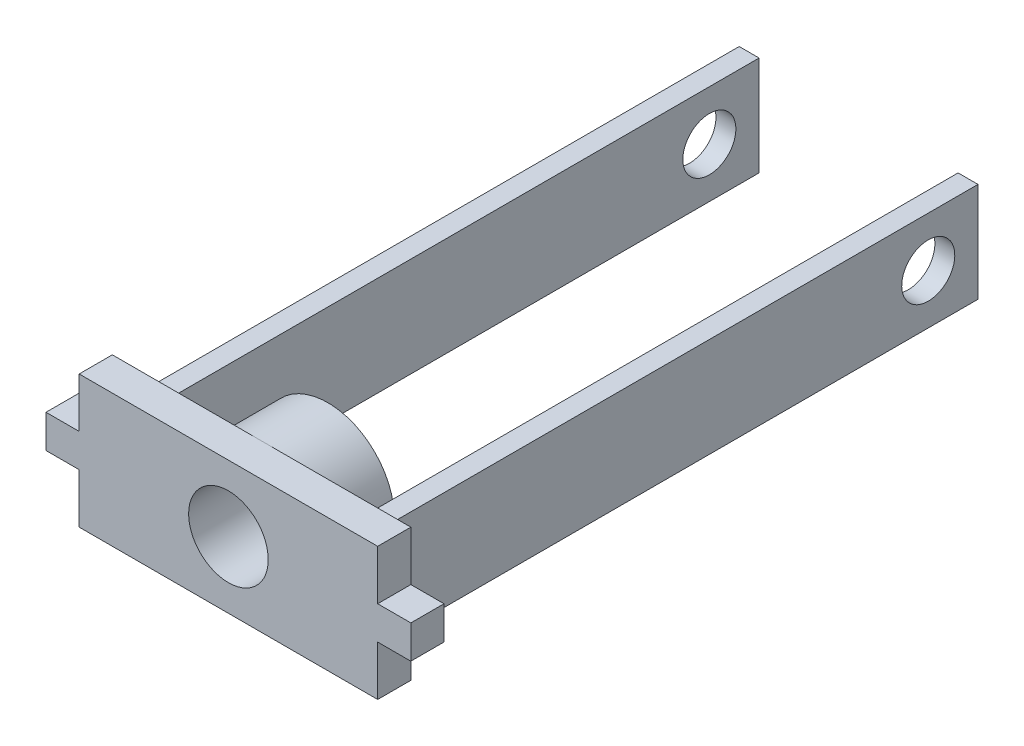
SolidWorks part; units mm, degrees
ref_plane "前基準面" through (0, 0, 0) normal (0, 0, 1) x (1, 0, 0)
ref_plane "上基準面" through (0, 0, 0) normal (0, 1, 0) x (1, 0, 0)
ref_plane "右基準面" through (0, 0, 0) normal (1, 0, 0) x (0, 0, -1)
sketch "草圖1" plane through (0, 0, 0) normal (0, 0, 1) x (1, 0, 0)
  line L0 (-22.5, -2.5) -> (-22.5, -10)
  line L1 (-22.5, 10) -> (22.5, 10)
  line L2 (-22.5, 10) -> (-22.5, 2.5)
  line L3 (-22.5, -10) -> (22.5, -10)
  line L4 (22.5, 10) -> (22.5, 2.5)
  line L5 (-22.5, 10) -> (22.5, -10) construction
  line L6 (-22.5, -10) -> (22.5, 10) construction
  line L7 (-22.5, 2.5) -> (-27.5, 2.5)
  line L9 (-22.5, -2.5) -> (-27.5, -2.5)
  line L10 (-27.5, 2.5) -> (-27.5, -2.5)
  line L11 (22.5, 2.5) -> (27.5, 2.5)
  line L13 (22.5, -2.5) -> (27.5, -2.5)
  line L14 (27.5, 2.5) -> (27.5, -2.5)
  line L15 (22.5, -2.5) -> (22.5, -10)
  line L16 (-27.5, 0) -> (27.5, 0) construction
  circle A0 centre (0, 0) radius 6
  point P0 (0, 0)
  dimension "D1" = 12
  dimension "D2" = 20
  dimension "D3" = 45
  dimension "D4" = 5
  dimension "D5" = 5
  dimension "D6" = 5
extrude "填料-伸長1" add sketch "草圖1" along normal blind 5
sketch "草圖2" plane through (0, 0, 0) normal (0, 0, -1) x (-1, 0, 0)
  line L0 (-22.5, 7.5) -> (22.5, 7.5) construction
  line L1 (-22.5, 2.5) -> (-22.5, 10) construction
  line L2 (22.5, 10) -> (22.5, 2.5) construction
  line L3 (-22.5, -7.5) -> (22.5, -7.5) construction
  line L4 (-22.5, -10) -> (-22.5, -2.5) construction
  line L5 (22.5, -2.5) -> (22.5, -10) construction
  line L7 (22.5, 10) -> (-22.5, 10) construction
  line L9 (-18, 7.5) -> (-15, 7.5)
  line L10 (-18, 7.5) -> (-18, -7.5)
  line L11 (-18, -7.5) -> (-15, -7.5)
  line L12 (-15, 7.5) -> (-15, -7.5)
  line L14 (15, 7.5) -> (18, 7.5)
  line L15 (15, 7.5) -> (15, -7.5)
  line L16 (15, -7.5) -> (18, -7.5)
  line L17 (18, 7.5) -> (18, -7.5)
  dimension "D1" = 15
  dimension "D2" = 2.5
  dimension "D3" = 3
  dimension "D4" = 30
  dimension "D5" = 15
extrude "填料-伸長2" add sketch "草圖2" along normal blind 90
sketch "草圖4" plane through (18, 0, 0) normal (1, 0, 0) x (0, 0, -1)
  line L0 (90, 7.5) -> (90, -7.5) construction
  line L1 (90, 7.5) -> (0, 7.5) construction
  circle A0 centre (82.5, 0) radius 4
  dimension "D2" = 8
  dimension "D1" = 7.5
  dimension "D3" = 7.5
extrude "除料-伸長1" cut sketch "草圖4" against normal through all
sketch "草圖5" plane through (0, 0, 0) normal (0, 0, -1) x (-1, 0, 0)
  circle A0 centre (0, 0) radius 6
  circle A1 centre (0, 0) radius 10
  dimension "D1" = 20
extrude "填料-伸長3" add sketch "草圖5" along normal blind 10
